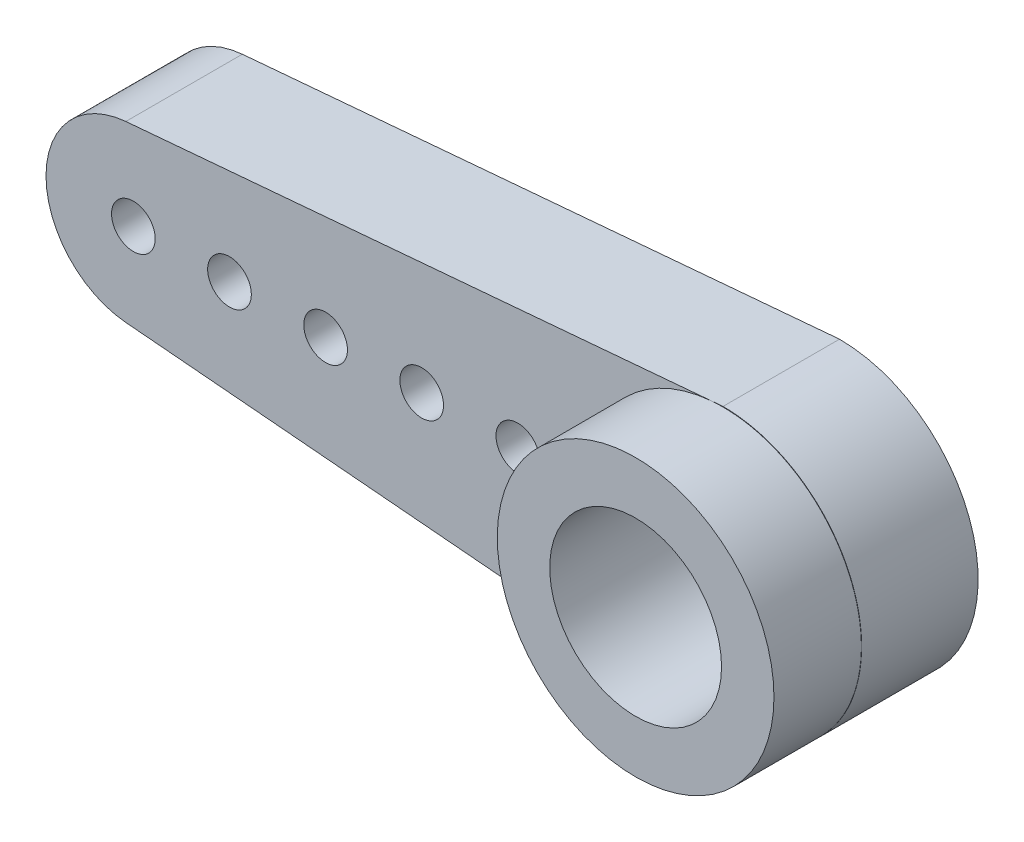
SolidWorks part; units mm, degrees
material "1060 Alloy"
ref_plane "Front Plane" through (0, 0, 0) normal (0, 0, 1) x (1, 0, 0)
ref_plane "Top Plane" through (0, 0, 0) normal (0, 1, 0) x (1, 0, 0)
ref_plane "Right Plane" through (0, 0, 0) normal (1, 0, 0) x (0, 0, -1)
sketch "Sketch1" plane through (0, 0, 0) normal (0, 0, 1) x (1, 0, 0)
  line L0 (0, 4.7678) -> (-20.5041, 2.9888)
  line L1 (-20.2447, 0) -> (0, 0) construction
  line L2 (-20.5041, -2.9888) -> (-0.4106, -4.7322)
  line L3 (-20.2447, 0) -> (-16.9447, 0) construction
  circle A0 centre (0, 0) radius 2.95
  circle A1 centre (0, 0) radius 4.75 construction
  circle A2 centre (-20.2447, 0) radius 3 construction
  arc A3 (-20.5041, 2.9888) -> (-20.5041, -2.9888) centre (-20.2447, 0) ccw
  arc A4 (0, 4.7678) -> (-0.4106, -4.7322) centre (0.0008, 0.0089) cw
  circle A8 centre (-20.2447, 0) radius 0.75
  circle A9 centre (-16.9447, 0) radius 0.75
  circle A10 centre (-13.6447, 0) radius 0.75
  circle A11 centre (-10.3447, 0) radius 0.75
  circle A12 centre (-7.0447, 0) radius 0.75
  point P11 (-23.2447, 0)
  point P13 (4.7553, -0.1966)
  dimension "D1" = 9.5
  dimension "D2" = 3
  dimension "D3" = 28
  dimension "D4" = 5.9
  dimension "D5" = 1.5
  dimension "D7" = 3.3
  dimension "D6" = 5
extrude "Boss-Extrude1" add sketch "Sketch1" along normal blind 4
sketch "Sketch2" plane through (0, 0, 4) normal (0, 0, 1) x (1, 0, 0)
  circle A0 centre (0, 0) radius 4.75
  circle A1 centre (0, 0) radius 2.95
  circle A2 centre (0, 0) radius 2.95 construction
  arc A3 (-0.4106, -4.7322) -> (0, 4.7678) centre (0.0008, 0.0089) ccw construction
extrude "Boss-Extrude2" add sketch "Sketch2" along normal blind 3
